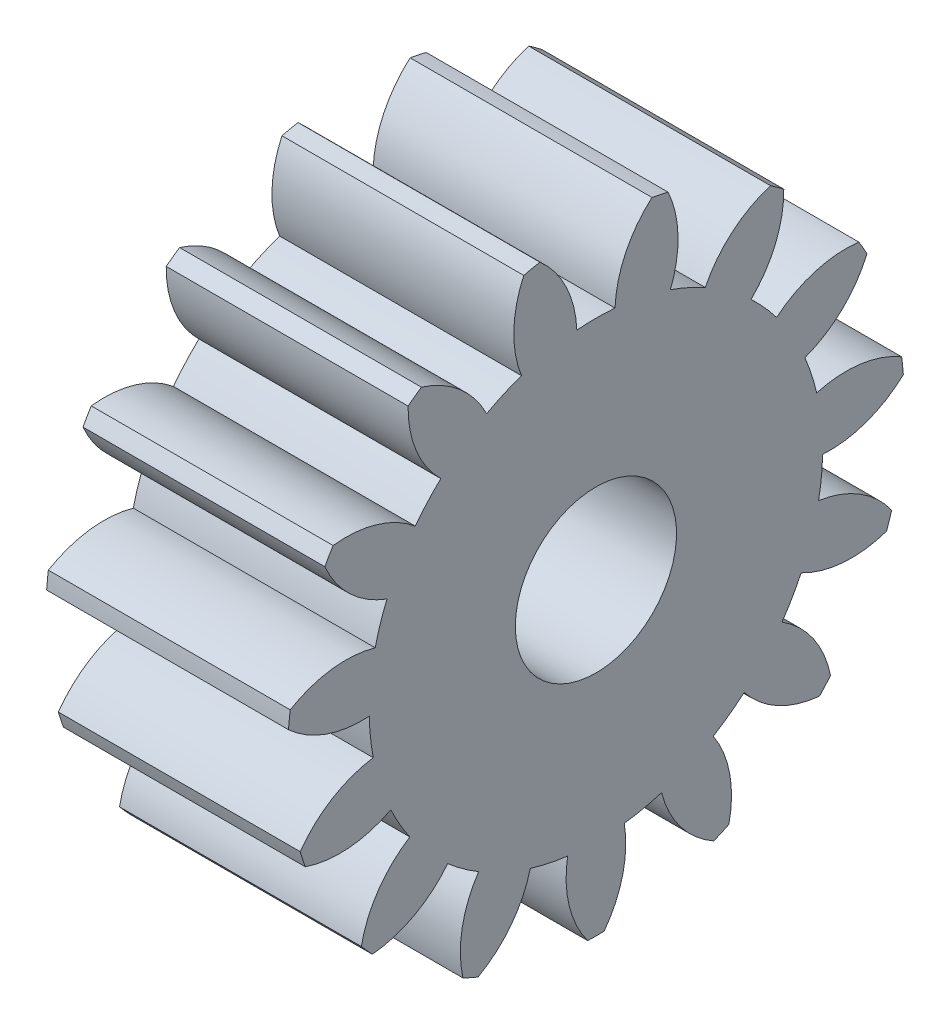
SolidWorks part; units mm, degrees
ref_plane "Plane1" through (0, 0, 0) normal (0, 0, 1) x (1, 0, 0)
ref_plane "Plane2" through (0, 0, 0) normal (0, 1, 0) x (1, 0, 0)
ref_plane "Plane3" through (0, 0, 0) normal (1, 0, 0) x (0, 0, -1)
sketch "HoldingSke" plane through (0, 0, 0) normal (0, 1, 0) x (1, 0, 0)
  line L0 (0, 0) -> (0.4293, -0.115)
  line L1 (-15, 0) -> (100, 0) construction
  line L2 (0, 0) -> (-2.1039, 2.3779)
  line L3 (0, 0) -> (-11.863, 4.5341)
  line L4 (0, 0) -> (8.3417, 2.2352)
  line L5 (0, 0) -> (-46.8476, -17.4728)
  line L6 (0, 0) -> (-12.4344, -8.3896)
  line L7 (-2.1039, 2.3779) -> (8.6586, 51.2059)
  line L8 (-76.2, 54.61) -> (-74.4, 54.61)
  line L9 (-71.009, 38.7566) -> (-53.1078, 45.2721)
  line L10 (-76.2, 71.12) -> (104.1128, 71.12)
  line L11 (0, 0) -> (-15, 0)
  line L12 (-76.2, 101.6) -> (-76.123, 101.6)
  line L13 (24.9733, 27.94) -> (52.9518, 28.4284)
  line L14 (24.9733, 27.94) -> (24.9743, 27.94)
  line L15 (24.9733, 27.94) -> (100.4006, 29.5858)
  line L16 (-63.627, -2.25) -> (-12.827, -2.25)
  circle A0 centre (0, 0) radius 5
  circle A1 centre (0, 0) radius 14.0615
  circle A2 centre (0, 0) radius 37.5
  circle A3 centre (0, 0) radius 5
  dimension "MHD" = 28.123
  dimension "Hub_dia" = 75
  dimension "Bore" = 10
  dimension "MBD" = 10
  dimension "Num_teeth" = 15
  dimension "Pitch_radius" = 180.3128
  dimension "Pitch" = 0.4444
  dimension "Width" = 15
  dimension "Overall_len" = 50
  dimension "Show_teeth" = 15
  dimension "Thickness" = 15
  dimension "OAL" = 50.0001
  dimension "T_dim" = 1.8
  dimension "Ap" = 20
  dimension "H" = 19.05
  dimension "Backlash" = 0.077
  dimension "Addendum_fac" = 1
  dimension "Dedendum_fac" = 1.25
  dimension "Clearance_fac" = 0.25
  dimension "Dedendum_add" = 0.001
  dimension "Module" = 2.25
sketch "BasProSke" plane through (0, 0, 0) normal (0, 1, 0) x (1, 0, 0)
  line L0 (-10, 0) -> (60, 0) construction
  line L1 (0, 0) -> (0, 19.125)
  line L2 (0, 0) -> (15, 0)
  line L3 (15, 0) -> (15, 19.125)
  line L4 (15, 19.125) -> (0, 19.125)
  dimension "Diameter" = 38.25
  dimension "Thickness" = 15
revolve "Base-Revolve" add sketch "BasProSke" angle 360 about L0
sketch "TooCutSke" plane through (0, 0, 0) normal (1, 0, 0) x (0, 0, -1)
  line L1 (0, 0) -> (0, 107) construction
  line L2 (0, 0) -> (-1.8986, 16.7679) construction
  line L3 (0, 0) -> (-6.9842, 32.8583) construction
  line L4 (-1.8986, 16.7679) -> (-3.4921, 16.4291) construction
  arc A0 (1.1837, 14.0116) -> (-1.1837, 14.0116) centre (0, 0) ccw
  arc A1 (3.4999, 18.8279) -> (-3.4999, 18.8279) centre (0, 0) ccw
  circle A2 centre (0, 0) radius 16.875 construction
  circle A3 centre (0, 0) radius 15.8573 construction
  arc A4 (-1.1837, 14.0116) -> (-3.4999, 18.8279) centre (-7.9279, 13.7332) ccw
  arc A5 (3.4999, 18.8279) -> (1.1837, 14.0116) centre (7.9279, 13.7332) ccw
  dimension "Root_dia" = 28.123
  dimension "Overcut_dia" = 38.3008
  dimension "Pitch_dia" = 33.75
  dimension "Base_dia" = 31.7146
  dimension "Flank_rad" = 6.75
  dimension "Half_ang" = 12
  dimension "Half_CT" = 1.6292
extrude "ToothCut" cut sketch "TooCutSke" along normal through all
fillet "Breaks" [suppressed] radius 0.045
fillet "RootFillets" [suppressed] radius 0.5635
pattern_circular "TeethCuts" count 15 every 24 about axis through (-10, 0, 0) along (1, 0, 0) of "ToothCut", "RootFillets", "Breaks"
sketch "HubNeaOneSke" plane through (0, 0, 0) normal (-1, 0, 0) x (0, 0, 1)
  circle A0 centre (0, 0) radius 14.0615
  dimension "Diameter" = 28.123
extrude "HubNearOne" [suppressed] add sketch "HubNeaOneSke" along normal blind 35.0001
sketch "HubNeaBotSke" plane through (0, 0, 0) normal (-1, 0, 0) x (0, 0, 1)
  circle A0 centre (0, 0) radius 14.0615
  dimension "Diameter" = 28.123
extrude "HubNearBoth" [suppressed] add sketch "HubNeaBotSke" along normal blind 17.5
ref_plane "FarPln" through (15, 0, 0) normal (1, 0, 0) x (0, 0, -1)
sketch "HubFarSke" plane through (15, 0, 0) normal (1, 0, 0) x (0, 0, -1)
  circle A0 centre (0, 0) radius 14.0615
  dimension "Diameter" = 28.123
extrude "HubFar" [suppressed] add sketch "HubFarSke" along normal blind 17.5
sketch "BorSke" plane through (0, 0, 0) normal (1, 0, 0) x (0, 0, -1)
  circle A0 centre (0, 0) radius 5
  dimension "Diameter" = 10
extrude "Bore" cut sketch "BorSke" along normal mid plane 100.0001
sketch "KeySke" plane through (0, 0, 0) normal (1, 0, 0) x (0, 0, -1)
  line L0 (-2, 0) -> (-2, 6.8)
  line L1 (-2, 6.8) -> (2, 6.8)
  line L2 (2, 6.8) -> (2, 0)
  line L3 (0, 0) -> (0, 34) construction
  line L4 (-2, 0) -> (2, 0)
  dimension "Offset" = 6.8
  dimension "Width" = 4
extrude "Keyway" [suppressed] cut sketch "KeySke" along normal mid plane 100.0001
pattern_circular "Keyway2" [suppressed] count 2 every 90 about axis through (-10, 0, 0) along (1, 0, 0)
equation "' \"Module@HoldingSke\" = 6.35"
equation "' \"Num_teeth@HoldingSke\" = 12"
equation "' \"Ap@HoldingSke\" =  20"
equation "' \"Width@HoldingSke\" = 0.5 * 25.4"
equation "' \"Hub_dia@HoldingSke\"= 1 * 25.4"
equation "' \"Overall_len@HoldingSke\" = 1.0 * 25.4"
equation "' \"Bore@HoldingSke\" = 0.75 * 25.4"
equation "' \"T_dim@HoldingSke\" = 0.1 * 25.4"
equation "' \"Width@KeySke\" = 0.25 * 25.4"
equation "' \"Show_teeth@HoldingSke\" = 13"
equation "' \"Backlash@HoldingSke\" = 0.009 * 25.4"
equation "' \"Addendum_fac@HoldingSke\" = 1.0"
equation "' \"Dedendum_fac@HoldingSke\" = 1.25"
equation "' \"Dedendum_add@HoldingSke\" = 0.00005 * 25.4"
equation "' \"Clearance_fac@HoldingSke\" = 0.25"
equation "\"Pitch@HoldingSke\" = 1 / \"Module@HoldingSke\""
equation "\"Overcut_dia@TooCutSke\" = (\"Num_teeth@HoldingSke\" + 2 * \"Addendum_fac@HoldingSke\") / \"Pitch@HoldingSke\" + 0.002 * 25.4"
equation "\"Pitch_dia@TooCutSke\" = \"Num_teeth@HoldingSke\" / \"Pitch@HoldingSke\""
equation "\"Base_dia@TooCutSke\" = \"Num_teeth@HoldingSke\" / \"Pitch@HoldingSke\" * cos((\"Ap@HoldingSke\"  * 3.14159265 / 180))"
equation "\"Root_dia@TooCutSke\" = (\"Num_teeth@HoldingSke\" + 2) / \"Pitch@HoldingSke\" - 2 * (\"Addendum_fac@HoldingSke\" + \"Dedendum_fac@HoldingSke\") / \"Pitch@HoldingSke\" - \"Dedendum_add@HoldingSke\" * 2"
equation "\"Half_ang@TooCutSke\" = 180 / \"Num_teeth@HoldingSke\""
equation "\"Half_CT@TooCutSke\" = \"Num_teeth@HoldingSke\" / \"Pitch@HoldingSke\" * sin((3.14159265 / 2 / \"Num_teeth@HoldingSke\")) / 2 - 7 * \"Backlash@HoldingSke\" / 4"
equation "\"Flank_rad@TooCutSke\" = \"Num_teeth@HoldingSke\" / \"Pitch@HoldingSke\" / 5"
equation "\"Radius@RootFillets\" = \"Clearance_fac@HoldingSke\" / \"Pitch@HoldingSke\" + \"Dedendum_add@HoldingSke\""
equation "\"Break_rad@Breaks\" = 0.02 / \"Pitch@HoldingSke\""
equation "\"Thickness@HoldingSke\" = \"Width@HoldingSke\""
equation "\"OAL@HoldingSke\" = \"Thickness@HoldingSke\""
equation "\"MHD@HoldingSke\" = (\"Num_teeth@HoldingSke\" + 2) / \"Pitch@HoldingSke\" - 2 * (\"Addendum_fac@HoldingSke\" + \"Dedendum_fac@HoldingSke\")  / \"Pitch@HoldingSke\" - \"Dedendum_add@HoldingSke\" * 2"
equation "\"MBD@HoldingSke\" = (\"Num_teeth@HoldingSke\" + 2) / \"Pitch@HoldingSke\" - 2 * (\"Addendum_fac@HoldingSke\" + \"Dedendum_fac@HoldingSke\")  / \"Pitch@HoldingSke\" - \"Dedendum_add@HoldingSke\" * 2 - 0.002 * 25.4"
equation "\"MHD@HoldingSke\" = ((sgn( \"MHD@HoldingSke\" - \"Hub_dia@HoldingSke\" )-1)*( \"MHD@HoldingSke\" - \"Hub_dia@HoldingSke\" ))/-2+ \"Hub_dia@HoldingSke\""
equation "\"MBD@HoldingSke\" = ((sgn( \"MBD@HoldingSke\" - \"Bore@HoldingSke\" )-1)*( \"MBD@HoldingSke\" - \"Bore@HoldingSke\" ))/-2+ \"Bore@HoldingSke\""
equation "\"OAL@HoldingSke\" = ((sgn( \"OAL@HoldingSke\" - \"Overall_len@HoldingSke\" )+1)*( \"OAL@HoldingSke\" - \"Overall_len@HoldingSke\" ))/2 + \"Overall_len@HoldingSke\" + 0.000002 * 25.4"
equation "\"Num_teeth@TeethCuts\" = int( \"Show_teeth@HoldingSke\" ) + 1"
equation "\"Num_teeth@TeethCuts\" = ((sgn( \"Num_teeth@TeethCuts\" - \"Num_teeth@HoldingSke\" )-1)*( \"Num_teeth@TeethCuts\" - \"Num_teeth@HoldingSke\" ))/-2+ \"Num_teeth@HoldingSke\""
equation "\"Num_teeth@TeethCuts\" = ((sgn( \"Num_teeth@TeethCuts\" - 2.0)+1)*( \"Num_teeth@TeethCuts\" - 2.0))/2 +2.0"
equation "\"Angle@TeethCuts\" = 360.0 / \"Num_teeth@HoldingSke\""
equation "\"Diameter@BasProSke\" = (\"Num_teeth@HoldingSke\" + 2 * \"Addendum_fac@HoldingSke\") / \"Pitch@HoldingSke\""
equation "\"Thickness@BasProSke\"  = \"Thickness@HoldingSke\""
equation "' \"Fillet_rad@BasProSke\" =  \"Thickness@HoldingSke\" * 0.05"
equation "\"MHD@HoldingSke\" = ((sgn( \"MHD@HoldingSke\" - \"Root_dia@TooCutSke\" )-1)*( \"MHD@HoldingSke\" - \"Root_dia@TooCutSke\" ))/-2+ \"Root_dia@TooCutSke\""
equation "\"Diameter@HubNeaOneSke\" = \"MHD@HoldingSke\""
equation "\"Length@HubNearOne\" = \"OAL@HoldingSke\" - \"Thickness@BasProSke\""
equation "\"Diameter@HubNeaBotSke\" = \"MHD@HoldingSke\""
equation "\"Length@HubNearBoth\" = ( \"OAL@HoldingSke\" - \"Thickness@BasProSke\" ) / 2.0"
equation "\"Thickness@FarPln\" = \"Thickness@BasProSke\""
equation "\"Diameter@HubFarSke\" = \"MHD@HoldingSke\""
equation "\"Length@HubFar\" = ( \"OAL@HoldingSke\" - \"Thickness@BasProSke\" ) / 2.0"
equation "\"Diameter@BorSke\" = \"MBD@HoldingSke\""
equation "\"D1@Bore\" = \"OAL@HoldingSke\" * 2.0"
equation "\"D1@Keyway\" = \"OAL@HoldingSke\" * 2.0"
equation "\"Offset@KeySke\" = \"T_dim@HoldingSke\" + \"MBD@HoldingSke\" / 2.0"
